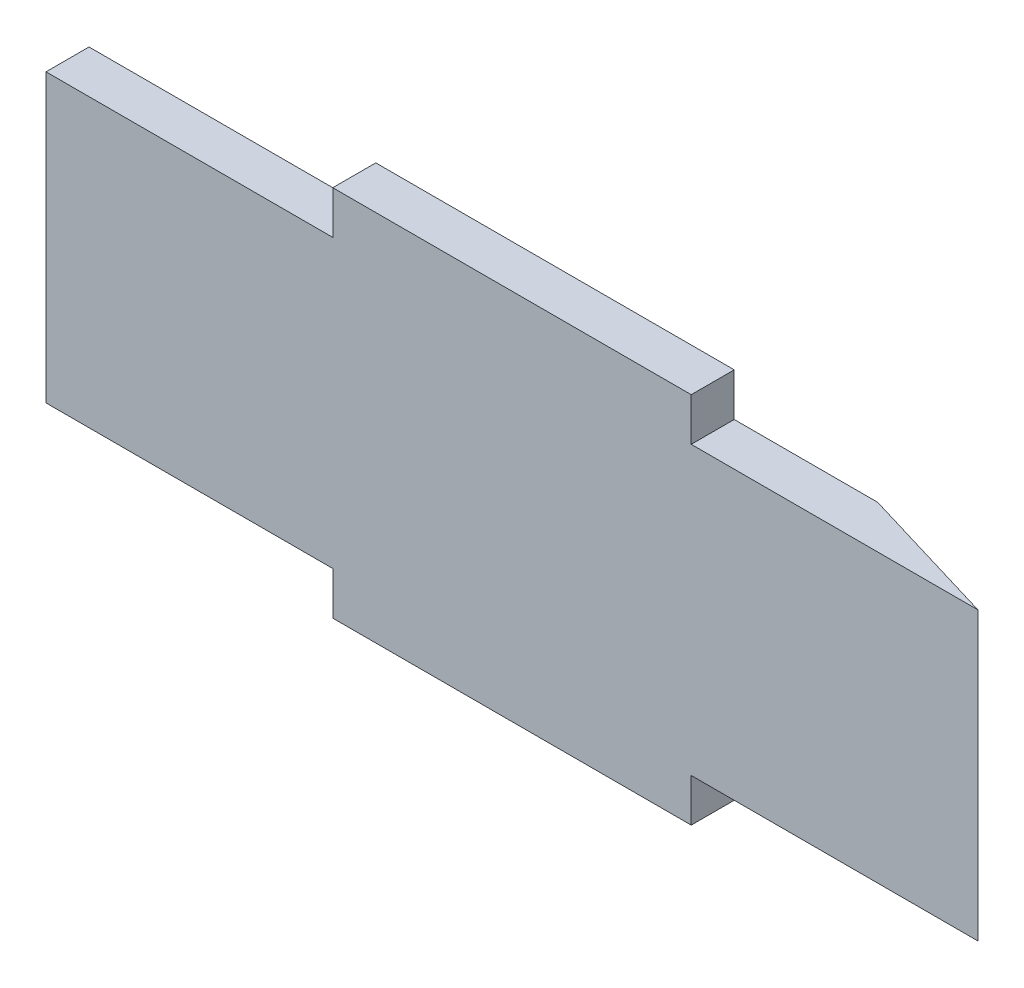
SolidWorks part; units mm, degrees
ref_plane "Plan de face" through (0, 0, 0) normal (0, 0, 1) x (1, 0, 0)
ref_plane "Plan de dessus" through (0, 0, 0) normal (0, 1, 0) x (1, 0, 0)
ref_plane "Plan de droite" through (0, 0, 0) normal (1, 0, 0) x (0, 0, -1)
sketch "Esquisse1" plane through (0, 0, 0) normal (0, 0, 1) x (1, 0, 0)
  line L1 (65, 20) -> (-65, 20)
  line L2 (65, 20) -> (65, -20)
  line L3 (65, -20) -> (-65, -20)
  line L4 (-65, 20) -> (-65, -20)
  line L5 (65, 20) -> (-65, -20) construction
  line L6 (65, -20) -> (-65, 20) construction
  point P0 (0, 0)
  dimension "D1" = 130
  dimension "D2" = 40
extrude "Boss.-Extru.1" add sketch "Esquisse1" along normal blind 6
sketch "Esquisse5" plane through (0, 0, 0) normal (0, 0, -1) x (-1, 0, 0)
  line L0 (-65, 20) -> (65, 20) construction
  line L1 (25, 20) -> (-25, 20)
  line L2 (25, 20) -> (25, 26)
  line L3 (25, 26) -> (-25, 26)
  line L4 (-25, 20) -> (-25, 26)
  line L5 (65, 20) -> (65, -20) construction
  line L6 (-65, 0) -> (65, 0) construction
  line L7 (-65, -20) -> (-65, 20) construction
  line L8 (25, -26) -> (-25, -26)
  line L9 (-25, -20) -> (-25, -26)
  line L10 (25, -20) -> (-25, -20)
  line L11 (25, -20) -> (25, -26)
  dimension "D1" = 50
  dimension "D2" = 40
  dimension "D3" = 6
extrude "Boss.-Extru.3" add sketch "Esquisse5" against normal blind 6
sketch "Esquisse6" plane through (0, -20, 0) normal (0, -1, 0) x (1, 0, 0)
  line L4 (65, 6) -> (45, 0)
  line L5 (25, 0) -> (65, 0) construction
  line L6 (45, 0) -> (65, 0)
  line L7 (65, 0) -> (65, 6)
extrude "Enlèv. mat.-Extru.1" cut sketch "Esquisse6" against normal through all
